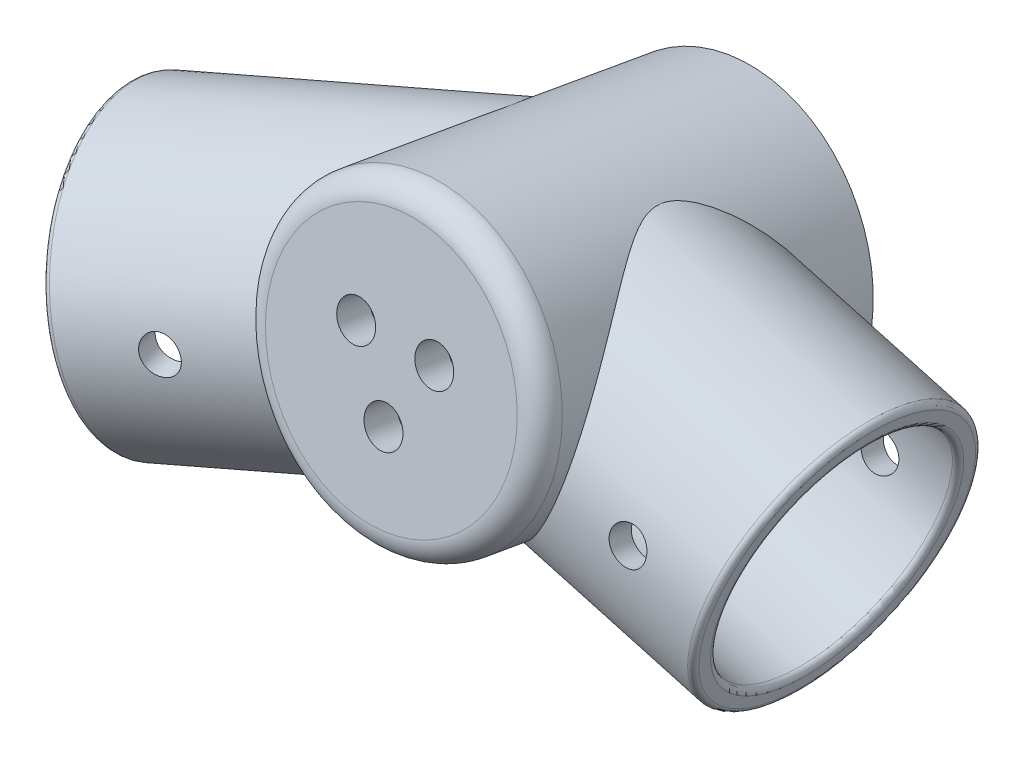
SolidWorks part; units mm, degrees
ref_plane "Front Plane" through (0, 0, 0) normal (0, 0, 1) x (1, 0, 0)
ref_plane "Top Plane" through (0, 0, 0) normal (0, 1, 0) x (1, 0, 0)
ref_plane "Right Plane" through (0, 0, 0) normal (1, 0, 0) x (0, 0, -1)
sketch "Sketch8" plane through (0, 0, 0) normal (0, 0, 1) x (1, 0, 0)
  line L0 (0, 0) -> (50000, 0) construction
ref_plane "Plane3" through (0, 0, 0) normal (0, 0.1736, 0.9848) x (1, 0, 0)
sketch "Sketch1" plane through (0, 0, 0) normal (0, 0.1736, 0.9848) x (1, 0, 0)
  circle A0 centre (0, 0) radius 13
  dimension "D1" = 26
extrude "Boss-Extrude1" add sketch "Sketch1" along normal blind 30
sketch "Sketch2" plane through (0, 0, 0) normal (0, 0.1736, 0.9848) x (1, 0, 0)
  circle A0 centre (0, 0) radius 8.5
  dimension "D1" = 17
extrude "Cut-Extrude1" cut sketch "Sketch2" along normal offset from surface (27 mm away) 3 up to face at (0, -7.5931, 31.8017)
sketch "Sketch3" plane through (0, 5.2094, 29.5442) normal (0, 0.1736, 0.9848) x (1, 0, 0)
  line L0 (0, 0) -> (0, -8) construction
  circle A2 centre (0, -4) radius 1.7
  circle A3 centre (0, 0) radius 8
  circle A4 centre (-3.4641, 2) radius 1.7
  circle A5 centre (3.4641, 2) radius 1.7
  point P7 (0, -4)
  point P13 (0, 0)
  dimension "D1" = 16
  dimension "D2" = 3.4
  dimension "D3" = 3
extrude "Cut-Extrude3" cut sketch "Sketch3" against normal through all contours A4 | A5 | A2 L0 | L0 A2
sketch "Sketch7" plane through (0, 0, 0) normal (0, 0, 1) x (1, 0, 0)
  line L0 (0, 0) -> (24.0896, -6.6852) construction
  dimension "D1" = 25
  dimension "D2" = 15.51
ref_plane "Plane1" through (24.0896, -6.6852, 0) normal (0.9636, -0.2674, 0) x (0, 0, -1)
sketch "Sketch9" plane through (24.0896, -6.6852, 0) normal (0.9636, -0.2674, 0) x (0, 0, -1)
  line L0 (2.1776, 12.8163) -> (-27.3667, 17.8361) construction
  line L1 (2.1776, 12.8163) -> (-27.3667, 17.8361) construction
  line L2 (-12.5945, 15.3262) -> (-16.9497, -10.3065) construction
  line L3 (-31.7218, -7.7966) -> (-2.1776, -12.8163) construction
  circle A0 centre (-14.7721, 2.5099) radius 10.35
  circle A1 centre (-14.7721, 2.5099) radius 12.35
  dimension "D1" = 20.7
  dimension "D2" = 2
extrude "Boss-Extrude3" add sketch "Sketch9" against normal up to surface (17.7134 mm away)
sketch "Sketch17" plane through (0, 0, 0) normal (0, 0.1736, 0.9848) x (1, 0, 0)
  line L0 (24.2076, -6.6158) -> (12.5401, -3.4272) construction
  circle A0 centre (0, 0) radius 13 construction
  circle A1 centre (0, 0) radius 13 construction
  circle A2 centre (18.3738, -5.0215) radius 1.5875
  ellipse E0 centre (24.7608, -6.767) end of major axis (21.5049, -18.6801) minor radius 0.5735 construction
  ellipse E1 centre (24.7608, -6.767) end of major axis (21.5049, -18.6801) minor radius 0.5735 construction
  dimension "D1" = 3.175
extrude "Cut-Extrude4" cut sketch "Sketch17" against normal through all both and the other way through all
sketch "Sketch16" plane through (0, 0, 0) normal (0, 0, 1) x (1, 0, 0)
  line L0 (0, 0) -> (0, 50000) construction
ref_plane "Plane5" through (0, 0, 0) normal (0.2406, 0, 0.9706) x (0, 1, 0)
sketch "Sketch10" plane through (0, 0, 0) normal (-0.2406, 0, -0.9706) x (-0.9706, 0, 0.2406)
  line L2 (0, 0) -> (33.6442, -9.6473)
  dimension "D1" = 35
  dimension "D2" = 16
ref_plane "Plane4" through (-32.6558, -9.6473, 8.0951) normal (-0.933, -0.2756, 0.2313) x (0.2246, 0.0559, 0.9728)
sketch "Sketch14" plane through (-32.6558, -9.6473, 8.0951) normal (-0.933, -0.2756, 0.2313) x (0.2246, 0.0559, 0.9728)
  line L1 (-2.301, -0.419) -> (26.732, 4.8681) construction
  line L2 (12.1874, 15.4332) -> (12.1874, -10.8974) construction
  line L4 (26.7039, 18.0768) -> (-2.3291, 12.7897) construction
  circle A2 centre (12.1874, 2.2679) radius 10.35
  circle A3 centre (12.1874, 2.2679) radius 12.35
  ellipse E0 centre (0, 0) end of major axis (2.3291, -12.7897) minor radius 2.3388 construction
  ellipse E1 centre (29.033, 5.2871) end of major axis (31.3621, -7.5025) minor radius 2.3388 construction
  spline S0 degree 3 poles (17.2744, 10.6936) (16.3726, 10.8668) (15.919, 10.9129) (15.2394, 10.8947) (15.0107, 10.8736) (14.5676, 10.8006) (14.3529, 10.7491) (13.9361, 10.6187) (13.7324, 10.5391) (13.3443, 10.36) (13.1595, 10.2607) (12.6259, 9.94) (12.296, 9.695) (11.672, 9.1674) (11.3795, 8.8859) (10.8181, 8.2954) (10.5488, 7.9854) (9.7707, 7.0234) (9.2932, 6.3434) (8.3945, 4.9116) (7.974, 4.1596) (7.3845, 2.9701) (7.1952, 2.5636) (6.8384, 1.7436) (6.6699, 1.3284) (6.3536, 0.4868) (6.2059, 0.0605) (5.9333, -0.8046) (5.808, -1.2458) (5.5886, -2.1215) (5.4939, -2.5577) (5.376, -3.2092) (5.3407, -3.4259) (5.2788, -3.8583) (5.252, -4.0745) (5.1424, -5.1364) (5.1291, -5.937) (5.2615, -7.433) (5.4038, -8.0861) (5.6643, -8.795) (5.7206, -8.9314) (5.8415, -9.1938) (5.9063, -9.3199) (6.11, -9.6774) (6.2588, -9.8897) (6.5794, -10.2683) (6.7513, -10.4347) (7.117, -10.7255) (7.3113, -10.85) (7.9117, -11.1587) (8.3391, -11.2828) (9.0186, -11.3723) (9.2515, -11.3858) (9.7312, -11.3827) (9.9786, -11.366) (10.7391, -11.2745) (11.2652, -11.1591) (12.1073, -10.9237) (12.3971, -10.8349) (13.0055, -10.6406) (13.3257, -10.5344) (14.002, -10.3171) (14.3587, -10.2056) (14.9468, -10.0456) (15.1508, -9.994) (15.568, -9.8987) (15.7825, -9.8548) (16.2245, -9.7758) (16.4525, -9.7407) (16.9028, -9.6811) (17.1274, -9.656) (17.5757, -9.6125) (17.8001, -9.5939) (18.2392, -9.5607) (18.455, -9.5459) (19.0939, -9.5032) (19.5103, -9.4763) (20.317, -9.4127) (20.7076, -9.3763) (21.8503, -9.242) (22.5743, -9.119) (23.6144, -8.8579) (23.9539, -8.7578) (24.6073, -8.5318) (24.9223, -8.4056) (25.8315, -7.9835) (26.3908, -7.6448) (27.1467, -7.0262) (27.3827, -6.8028) (27.8145, -6.324) (28.0113, -6.0679) (28.3631, -5.5188) (28.5189, -5.2237) (28.7774, -4.6064) (28.8811, -4.2834) (28.9966, -3.7762) (29.0283, -3.6034) (29.0779, -3.2498) (29.0957, -3.0682) (29.127, -2.5181) (29.1186, -2.1445) (29.0452, -1.3845) (28.9801, -0.9979) (28.793, -0.2117) (28.6702, 0.1888) (28.3778, 0.9759) (28.2074, 1.366) (27.8221, 2.1394) (27.6062, 2.5242) (26.8993, 3.6597) (26.362, 4.3746) (25.1777, 5.7335) (24.5259, 6.3805) (23.1632, 7.5665) (22.4484, 8.1116) (21.3234, 8.8566) (20.9386, 9.093) (20.1595, 9.533) (19.7642, 9.7374) (18.9586, 10.1105) (18.5484, 10.2793) (17.7061, 10.5706) (17.2744, 10.6936) (16.3726, 10.8668) (15.919, 10.9129) knots -0.015625 -0.015625 0 0 0.015625 0.015625 0.023438 0.023438 0.03125 0.03125 0.039062 0.039062 0.046875 0.046875 0.0625 0.0625 0.078125 0.078125 0.09375 0.09375 0.125 0.125 0.15625 0.15625 0.171875 0.171875 0.1875 0.1875 0.203125 0.203125 0.21875 0.21875 0.234375 0.234375 0.242187 0.242187 0.25 0.25 0.28125 0.28125 0.3125 0.3125 0.320312 0.320312 0.328125 0.328125 0.34375 0.34375 0.359375 0.359375 0.375 0.375 0.40625 0.40625 0.421875 0.421875 0.4375 0.4375 0.46875 0.46875 0.484375 0.484375 0.5 0.5 0.515625 0.515625 0.523437 0.523437 0.53125 0.53125 0.539062 0.539062 0.546875 0.546875 0.554687 0.554687 0.5625 0.5625 0.578125 0.578125 0.59375 0.59375 0.625 0.625 0.640625 0.640625 0.65625 0.65625 0.6875 0.6875 0.703125 0.703125 0.71875 0.71875 0.734375 0.734375 0.75 0.75 0.757812 0.757812 0.765625 0.765625 0.78125 0.78125 0.796875 0.796875 0.8125 0.8125 0.828125 0.828125 0.84375 0.84375 0.875 0.875 0.90625 0.90625 0.9375 0.9375 0.953125 0.953125 0.96875 0.96875 0.984375 0.984375 1 1 1.015625 1.015625 1.023438 only from (16.8235, 10.7802) to (16.8235, 10.7802) construction
  dimension "D1" = 20.7
  dimension "D2" = 2
extrude "Boss-Extrude4" add sketch "Sketch14" against normal up to surface (24.7995 mm away)
sketch "Sketch18" plane through (0, 0, 0) normal (0.2406, 0, 0.9706) x (0, 1, 0)
  line L0 (5.0821, 37.8678) -> (-18.6611, 31.0595) construction
  line L1 (5.0821, 37.8678) -> (-18.6611, 31.0595) construction
  line L2 (-6.7895, 34.4636) -> (5.2094, 7.1086) construction
  line L3 (-6.7895, 34.4636) -> (0.0483, 18.8749) construction
  circle A0 centre (-3.3706, 26.6693) radius 1.5875
  ellipse E1 centre (5.2094, 7.1086) end of major axis (15.6952, -0.5757) minor radius 12.4264 construction
  ellipse E2 centre (5.2094, 7.1086) end of major axis (15.6952, -0.5757) minor radius 12.4264 construction
  dimension "D1" = 3.175
extrude "Cut-Extrude5" cut sketch "Sketch18" against normal through all both and the other way through all
fillet "Fillet2" radius 0.5 4 edges at (28.0632, 7.6336, 14.7721) (27.5284, 5.7064, 14.7721) (-27.0565, -18.6334, 19.9736) (-27.6231, -16.7154, 19.9736)
fillet "Fillet3" radius 2 1 edges at (0, -7.5931, 31.8017)
mirror "Mirror1" [suppressed] about plane through (0, 0, 0) normal (0, 0, 1)
delete or keep bodies "Body-Delete/Keep 1" [suppressed] type delete bodies bodies 108
